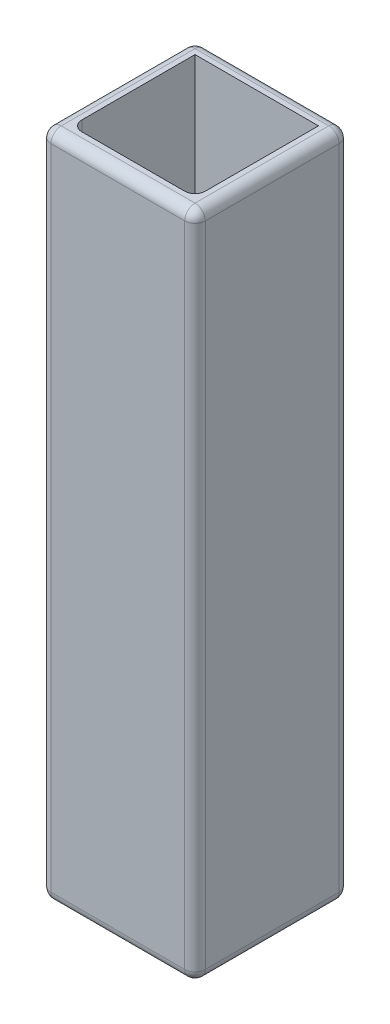
SolidWorks part; units mm, degrees
ref_plane "Alzado" through (0, 0, 0) normal (0, 0, 1) x (1, 0, 0)
ref_plane "Planta" through (0, 0, 0) normal (0, 1, 0) x (1, 0, 0)
ref_plane "Vista lateral" through (0, 0, 0) normal (1, 0, 0) x (0, 0, -1)
sketch "Croquis1" plane through (0, 0, 0) normal (0, 1, 0) x (1, 0, 0)
  line L1 (-15, 15) -> (15, 15)
  line L2 (-15, 15) -> (-15, -15)
  line L3 (-15, -15) -> (15, -15)
  line L4 (15, 15) -> (15, -15)
  line L5 (-15, 15) -> (15, -15) construction
  line L6 (-15, -15) -> (15, 15) construction
  line L7 (-12, 12) -> (12, 12)
  line L8 (-12, 12) -> (-12, -12)
  line L9 (-12, -12) -> (12, -12)
  line L10 (12, 12) -> (12, -12)
  line L11 (-12, 12) -> (12, -12) construction
  line L12 (-12, -12) -> (12, 12) construction
  point P0 (0, 0)
  point P6 (0, 0)
  dimension "D1" = 30
  dimension "D2" = 3
  dimension "D3" = 30
extrude "Saliente-Extruir1" add sketch "Croquis1" along normal blind 130
fillet "Redondeo2" radius 2 14 edges at (-12, 65, 12) (12, 65, 12) (-15, 65, -15) (-15, 65, 15) (15, 65, -15) (15, 65, 15) (-15, 130, 0) (0, 130, 15) (15, 130, 0) (0, 130, -15) (0, 0, 15) (15, 0, 0) (-15, 0, 0) (0, 0, -15)
